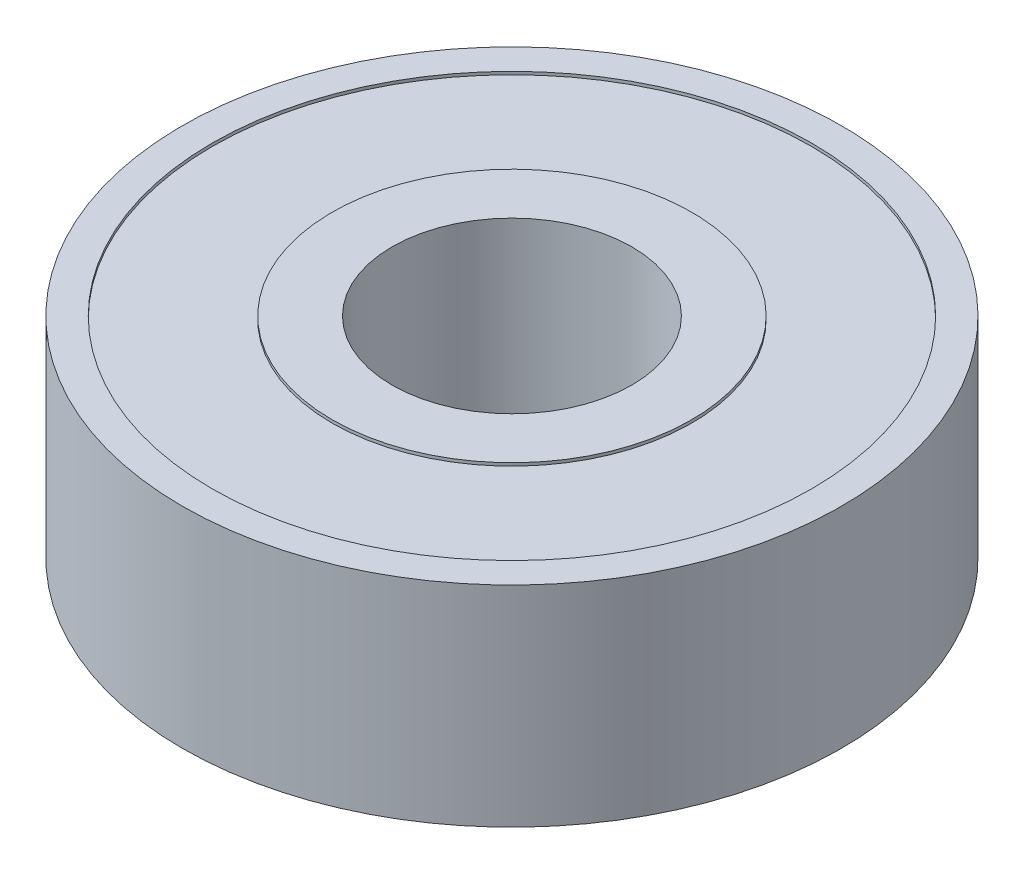
SolidWorks part; units mm, degrees
material "Stainless Steel (ferritic)"
ref_plane "Front Plane" through (0, 0, 0) normal (0, 0, 1) x (1, 0, 0)
ref_plane "Top Plane" through (0, 0, 0) normal (0, 1, 0) x (1, 0, 0)
ref_plane "Right Plane" through (0, 0, 0) normal (1, 0, 0) x (0, 0, -1)
sketch "Sketch1" plane through (0, 0, 0) normal (0, 1, 0) x (1, 0, 0)
  circle A0 centre (0, 0) radius 4
  circle A1 centre (0, 0) radius 11
  dimension "D1" = 8
  dimension "D2" = 22
extrude "Boss-Extrude1" add sketch "Sketch1" along normal mid plane 7
sketch "Sketch2" plane through (0, 3.5, 0) normal (0, 1, 0) x (1, 0, 0)
  circle A0 centre (0, 0) radius 10
  circle A1 centre (0, 0) radius 6
  circle A2 centre (0, 0) radius 4 construction
  circle A3 centre (0, 0) radius 11 construction
  dimension "D1" = 2
  dimension "D2" = 1
extrude "Cut-Extrude1" cut sketch "Sketch2" against normal blind 0.1
mirror "Mirror1" about plane through (0, 0, 0) normal (0, 1, 0) of "Cut-Extrude1"
